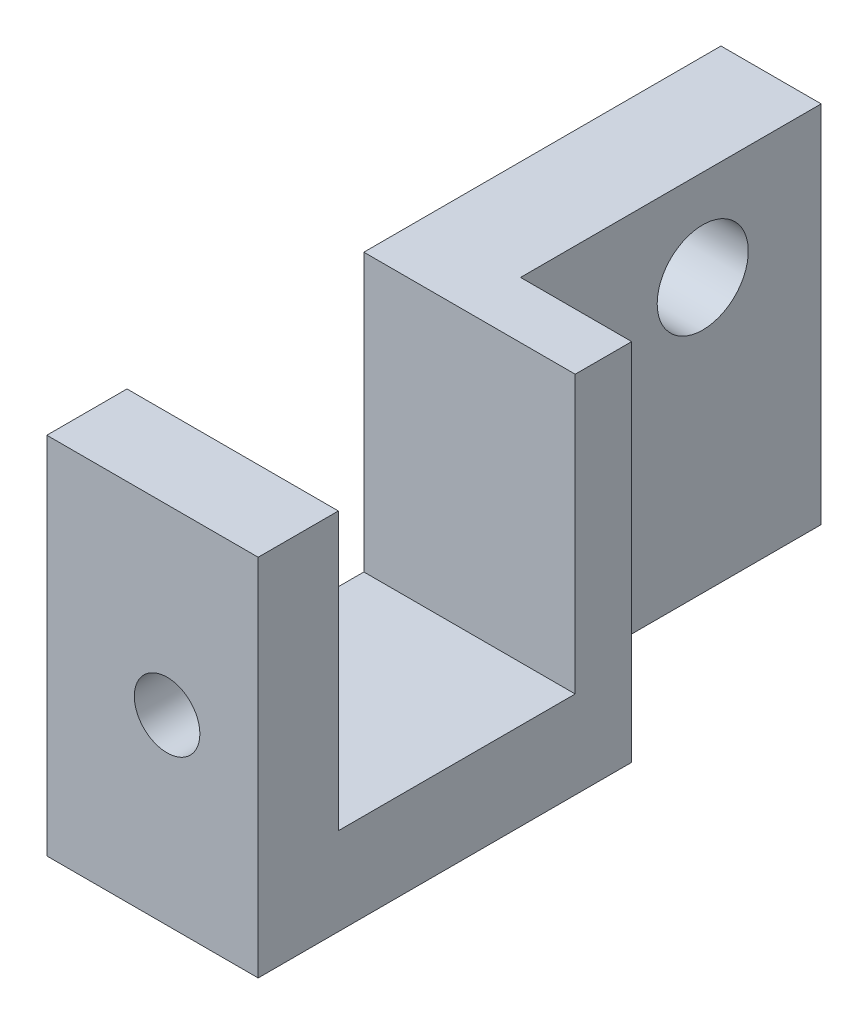
SolidWorks part; units mm, degrees
ref_plane "Front Plane" through (0, 0, 0) normal (0, 0, 1) x (1, 0, 0)
ref_plane "Top Plane" through (0, 0, 0) normal (0, 1, 0) x (1, 0, 0)
ref_plane "Right Plane" through (0, 0, 0) normal (1, 0, 0) x (0, 0, -1)
sketch "Sketch1" plane through (0, 0, 0) normal (0, 1, 0) x (1, 0, 0)
  line L1 (-7.366, 23.495) -> (7.366, 23.495)
  line L2 (-7.366, 23.495) -> (-7.366, -23.495)
  line L3 (-7.366, -23.495) -> (7.366, -23.495)
  line L4 (7.366, 23.495) -> (7.366, -23.495)
  dimension "D1" = 7.366
  dimension "D2" = 7.366
  dimension "D3" = 23.495
  dimension "D4" = 23.495
extrude "Boss-Extrude1" add sketch "Sketch1" along normal mid plane 25.4
sketch "Sketch2" plane through (7.366, 0, 0) normal (1, 0, 0) x (0, 0, -1)
  line L0 (-23.495, 12.7) -> (23.495, 12.7) construction
  line L1 (-17.907, 12.7) -> (-1.397, 12.7)
  line L2 (-17.907, 12.7) -> (-17.907, -6.604)
  line L3 (-17.907, -6.604) -> (-1.397, -6.604)
  line L4 (-1.397, 12.7) -> (-1.397, -6.604)
  line L5 (-23.495, 12.7) -> (-23.495, -12.7) construction
  line L6 (-23.495, -12.7) -> (23.495, -12.7) construction
  dimension "D1" = 5.588
  dimension "D2" = 16.51
  dimension "D3" = 6.096
extrude "Cut-Extrude1" cut sketch "Sketch2" against normal through all
sketch "Sketch3" plane through (0, 0, 23.495) normal (0, 0, 1) x (1, 0, 0)
  line L0 (-7.366, -12.7) -> (7.366, -12.7) construction
  line L1 (7.366, 12.7) -> (7.366, -12.7) construction
  circle A0 centre (1.016, 0) radius 2.286
  dimension "D1" = 12.7
  dimension "D2" = 6.35
extrude "Cut-Extrude2" cut sketch "Sketch3" against normal up to next
sketch "Sketch4" plane through (0, 0, -23.495) normal (0, 0, -1) x (-1, 0, 0)
  line L0 (-7.366, -12.7) -> (7.366, -12.7) construction
  line L1 (-7.366, 12.7) -> (0.381, 12.7)
  line L2 (-7.366, 12.7) -> (-7.366, -12.7)
  line L3 (-7.366, -12.7) -> (0.381, -12.7)
  line L4 (0.381, 12.7) -> (0.381, -12.7)
  dimension "D1" = 7.747
extrude "Cut-Extrude3" cut sketch "Sketch4" against normal blind 20.955
sketch "Sketch5" plane through (-7.366, 0, 0) normal (-1, 0, 0) x (0, 0, 1)
  line L0 (23.495, 12.7) -> (23.495, -12.7) construction
  line L1 (-23.495, 12.7) -> (1.397, 12.7) construction
  circle A0 centre (-15.24, 6.35) radius 3.175
  dimension "D1" = 38.735
  dimension "D2" = 6.35
extrude "Cut-Extrude4" cut sketch "Sketch5" against normal through all
